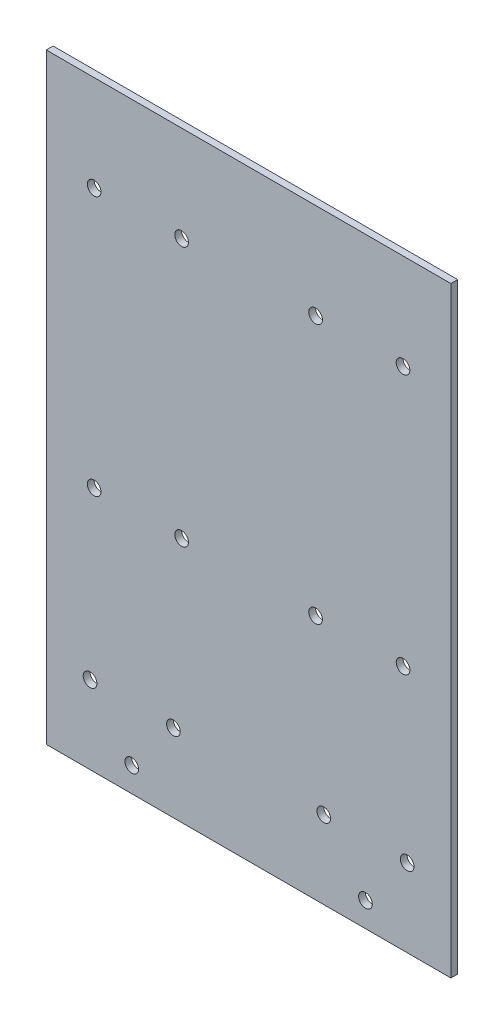
SolidWorks part; units mm, degrees
ref_plane "前视基准面" through (0, 0, 0) normal (0, 0, 1) x (1, 0, 0)
ref_plane "上视基准面" through (0, 0, 0) normal (0, 1, 0) x (1, 0, 0)
ref_plane "右视基准面" through (0, 0, 0) normal (1, 0, 0) x (0, 0, -1)
sketch "草图1" plane through (0, 0, 0) normal (0, 0, 1) x (1, 0, 0)
  line L0 (0, -110) -> (0, 110) construction
  line L1 (74, -110) -> (-74, -110)
  line L2 (74, -110) -> (74, 110)
  line L3 (74, 110) -> (-74, 110)
  line L4 (-74, -110) -> (-74, 110)
  line L5 (74, -110) -> (-74, 110) construction
  line L6 (74, 110) -> (-74, -110) construction
  circle A0 centre (-58, -81.5) radius 2.5
  circle A1 centre (-27.5, -81.5) radius 2.5
  circle A2 centre (-42.75, -101) radius 2.5
  circle A3 centre (42.75, -101) radius 2.5
  circle A4 centre (58, -81.5) radius 2.5
  circle A5 centre (27.5, -81.5) radius 2.5
  point P0 (0, 0)
  dimension "D3" = 5
  dimension "D4" = 5
  dimension "D5" = 5
  dimension "D6" = 9
  dimension "D7" = 16
  dimension "D8" = 30.5
  dimension "D9" = 19.5
  dimension "D10" = 15.25
  dimension "D1" = 148
  dimension "D2" = 220
extrude "凸台-拉伸1" add sketch "草图1" along normal blind 2.5
sketch "草图2" plane through (0, 0, 2.5) normal (0, 0, 1) x (1, 0, 0)
  line L0 (-74, 110) -> (-74, -110) construction
  line L1 (-74, -110) -> (74, -110) construction
  line L2 (0, 110) -> (0, -110) construction
  line L3 (74, 110) -> (-74, 110) construction
  circle A0 centre (-56.5, -20) radius 2.5
  circle A1 centre (-24.5, -20) radius 2.5
  circle A2 centre (-56.5, 75) radius 2.5
  circle A3 centre (-24.5, 75) radius 2.5
  circle A4 centre (-56.5, 170) radius 2.5
  circle A5 centre (-24.5, 170) radius 2.5
  circle A6 centre (24.5, 170) radius 2.5
  circle A7 centre (56.5, 170) radius 2.5
  circle A8 centre (24.5, 75) radius 2.5
  circle A9 centre (56.5, 75) radius 2.5
  circle A10 centre (24.5, -20) radius 2.5
  circle A11 centre (56.5, -20) radius 2.5
  dimension "D1" = 5
  dimension "D2" = 5
  dimension "D3" = 32
  dimension "D4" = 17.5
  dimension "D5" = 90
  dimension "D7" = 90
  dimension "D6" = 3
extrude "切除-拉伸1" cut sketch "草图2" against normal blind 3
